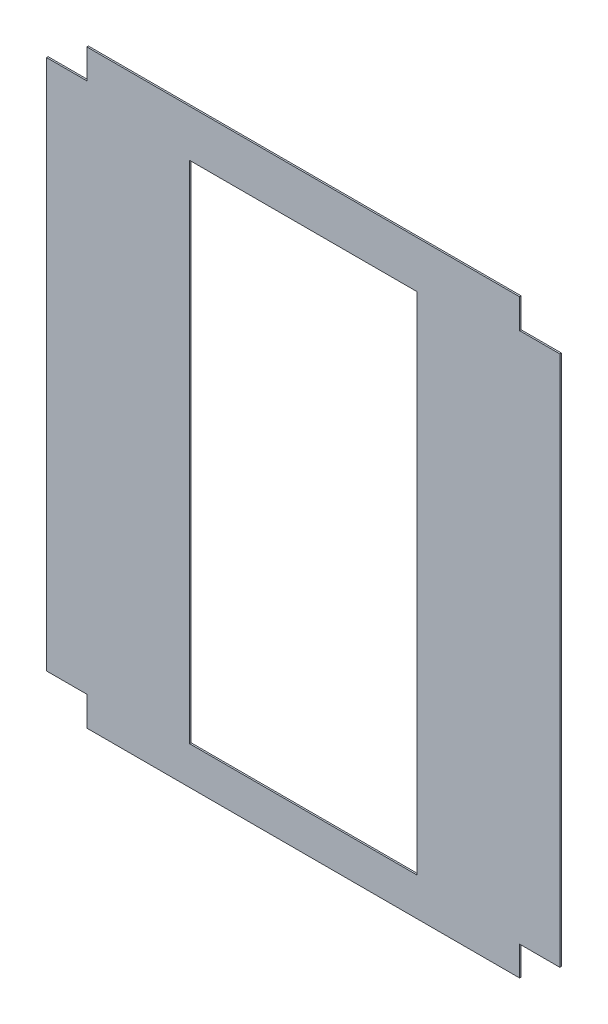
SolidWorks part; units mm, degrees
material "AISI 1020"
ref_plane "Front Plane" through (0, 0, 0) normal (0, 0, 1) x (1, 0, 0)
ref_plane "Top Plane" through (0, 0, 0) normal (0, 1, 0) x (1, 0, 0)
ref_plane "Right Plane" through (0, 0, 0) normal (1, 0, 0) x (0, 0, -1)
sketch "Sketch1" plane through (0, 0, 0) normal (0, 0, 1) x (1, 0, 0)
  line L0 (686.5297, 1180.7856) -> (686.5297, 1062.6756)
  line L5 (686.5297, 1062.6756) -> (848.5817, 1062.6756)
  line L6 (848.5817, -1073.9522) -> (686.5297, -1073.9522)
  line L11 (686.5297, -1073.9522) -> (686.5297, -1192.0622)
  line L17 (-1053.973, -1192.0622) -> (-1053.973, -1073.9522)
  line L18 (-1053.973, -1073.9522) -> (-1216.025, -1073.9522)
  line L23 (-1216.025, -1073.9522) -> (-1216.025, 1062.6756)
  line L24 (-1216.025, 1062.6756) -> (-1053.973, 1062.6756)
  line L29 (-1053.973, 1062.6756) -> (-1053.973, 1180.7856)
  line L30 (-1053.973, 1180.7856) -> (686.5297, 1180.7856)
  line L31 (848.5817, 1062.6756) -> (848.5817, -1073.9522)
  line L32 (-1053.973, -1192.0622) -> (-436.4479, -1192.0622)
  line L34 (-640.715, 992.3378) -> (273.685, 992.3378)
  line L36 (477.9521, -1192.0622) -> (686.5297, -1192.0622)
  line L37 (-436.4479, -1192.0622) -> (477.9521, -1192.0622)
  line L38 (-640.715, -1039.6622) -> (273.685, -1039.6622)
  line L39 (-640.715, -1039.6622) -> (-640.715, 992.3378)
  line L40 (273.685, 992.3378) -> (273.685, -1039.6622)
  point P17 (0, 0)
  dimension "D1" = 118.11
  dimension "D2" = 162.052
  dimension "D3" = 162.052
  dimension "D4" = 118.11
  dimension "D5" = 162.052
  dimension "D6" = 118.11
  dimension "D7" = 118.11
  dimension "D8" = 162.052
  dimension "D9" = 914.4
  dimension "D10" = 152.4
  dimension "D11" = 2032
  dimension "D12" = 575.31
  dimension "D13" = 2064.6067
extrude "Boss-Extrude2" add sketch "Sketch1" along normal blind 6.35
